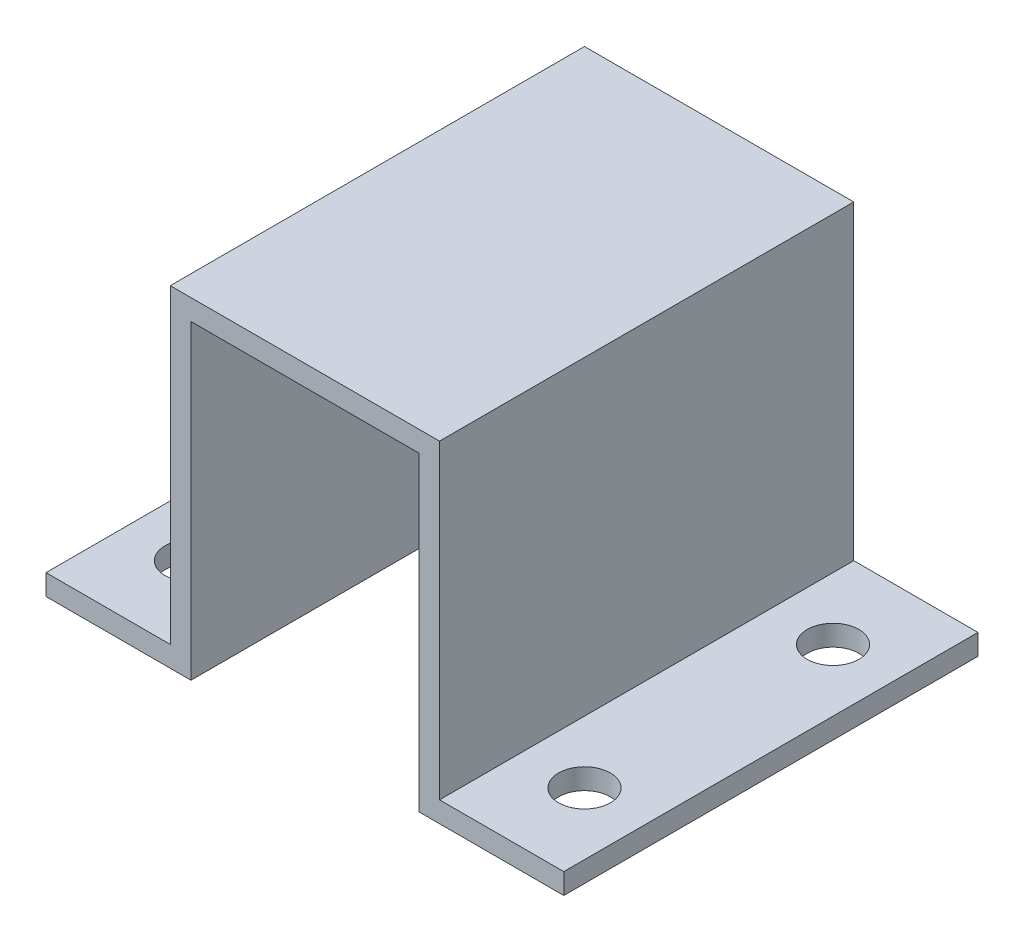
SolidWorks part; units mm, degrees
material "Plain Carbon Steel"
ref_plane "Front Plane" through (0, 0, 0) normal (0, 0, 1) x (1, 0, 0)
ref_plane "Top Plane" through (0, 0, 0) normal (0, 1, 0) x (1, 0, 0)
ref_plane "Right Plane" through (0, 0, 0) normal (1, 0, 0) x (0, 0, -1)
sketch "Sketch5" plane through (0, 0, 0) normal (0, 0, 1) x (1, 0, 0)
  line L0 (0, 0) -> (17.78, 0)
  line L1 (17.78, 0) -> (17.78, 38.1)
  line L2 (17.78, 38.1) -> (31.75, 38.1)
  line L3 (0, 0) -> (0, 2.54)
  line L4 (0, 2.54) -> (15.24, 2.54)
  line L5 (15.24, 2.54) -> (15.24, 40.64)
  line L6 (15.24, 40.64) -> (31.75, 40.64)
  line L7 (31.75, 40.64) -> (31.75, 38.1)
  line L8 (15.24, 2.54) -> (17.78, 2.54) construction
  dimension "D1" = 31.75
  dimension "D2" = 17.78
  dimension "D3" = 2.54
  dimension "D4" = 35.56
extrude "Boss-Extrude3" add sketch "Sketch5" along normal blind 50.8
mirror "Mirror6" about plane through (31.75, 40.64, 50.8) normal (-1, 0, 0) of "Boss-Extrude3"
sketch "Sketch6" plane through (0, 2.54, 0) normal (0, 1, 0) x (-1, 0, 0)
  line L0 (-7.62, 50.8) -> (-7.62, 40.64) construction
  line L2 (-7.62, 0) -> (-7.62, 10.16) construction
  line L4 (-55.88, 50.8) -> (-55.88, 40.64) construction
  line L6 (-55.88, 0) -> (-55.88, 10.16) construction
  line L9 (-55.88, 40.64) -> (-63.5, 40.64) construction
  line L10 (-63.5, 50.8) -> (-63.5, 0) construction
  line L11 (-55.88, 10.16) -> (-63.5, 10.16) construction
  line L12 (-7.62, 10.16) -> (0, 10.16) construction
  line L13 (0, 50.8) -> (0, 0) construction
  line L14 (-7.62, 40.64) -> (0, 40.64) construction
  line L15 (-15.24, 0) -> (0, 0) construction
  line L16 (-15.24, 50.8) -> (0, 50.8) construction
  circle A0 centre (-7.62, 40.64) radius 3.175
  circle A1 centre (-7.62, 10.16) radius 3.175
  circle A2 centre (-55.88, 10.16) radius 3.175
  circle A3 centre (-55.88, 40.64) radius 3.175
  dimension "D2" = 6.35
  dimension "D1" = 10.16
  dimension "D3" = 7.62
extrude "Cut-Extrude1" cut sketch "Sketch6" against normal up to next
